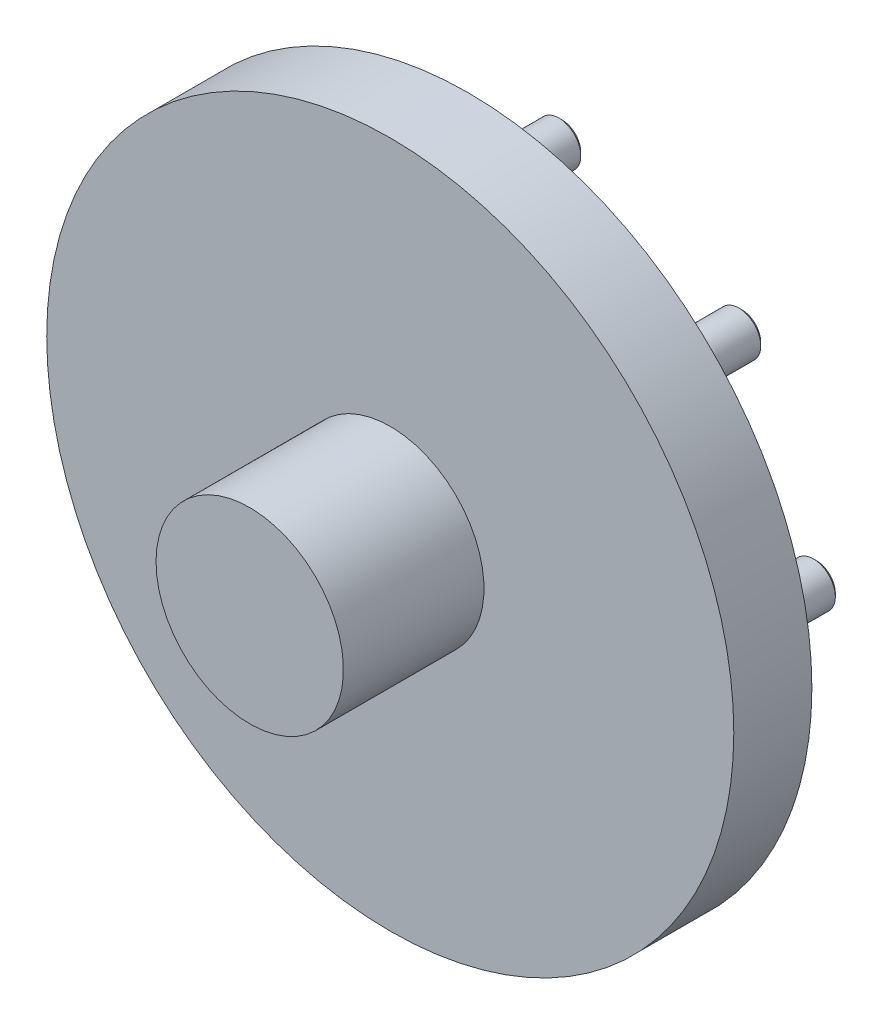
SolidWorks part; units mm, degrees
ref_plane "Front Plane" through (0, 0, 0) normal (0, 0, 1) x (1, 0, 0)
ref_plane "Top Plane" through (0, 0, 0) normal (0, 1, 0) x (1, 0, 0)
ref_plane "Right Plane" through (0, 0, 0) normal (1, 0, 0) x (0, 0, -1)
sketch "Sketch6" plane through (0, 0, 0) normal (0, -1, 0) x (1, 0, 0)
  line L0 (30, 75) -> (0, 75)
  line L1 (0, 75) -> (0, 0)
  line L2 (0, 0) -> (53, 0)
  line L3 (53, 0) -> (53, 5)
  line L4 (53, 5) -> (110, 5)
  line L5 (110, 5) -> (110, 30)
  line L6 (110, 30) -> (30, 30)
  line L7 (30, 30) -> (30, 75)
  line L8 (0, 75) -> (0, 0) construction
  dimension "D1" = 75
  dimension "D2" = 53
  dimension "D3" = 30
  dimension "D4" = 45
  dimension "D5" = 25
  dimension "D6" = 57
revolve "Revolve2" add sketch "Sketch6" angle 360 about L1
sketch "Sketch7" plane through (0, 0, 5) normal (0, 0, -1) x (-1, 0, 0)
  line L0 (0, 0) -> (0, -81.5) construction
  circle A0 centre (-57.6292, -57.6292) radius 7
  circle A1 centre (-81.5, 0) radius 7
  circle A2 centre (-57.6292, 57.6292) radius 7
  circle A3 centre (0, 81.5) radius 7
  circle A4 centre (57.6292, 57.6292) radius 7
  circle A5 centre (81.5, 0) radius 7
  circle A6 centre (0, -81.5) radius 7
  circle A7 centre (57.6292, -57.6292) radius 7
  dimension "D2" = 14
  dimension "D1" = 81.5
  dimension "D3" = 8
extrude "Boss-Extrude2" add sketch "Sketch7" along normal blind 30
chamfer "Chamfer2" distance 1 angle 45 8 edges at (-7, -81.5, -25) (-88.5, 0, -25) (50.6292, 57.6292, -25) (74.5, 0, -25) (50.6292, -57.6292, -25) (-64.6292, -57.6292, -25) (-64.6292, 57.6292, -25) (-7, 81.5, -25)
